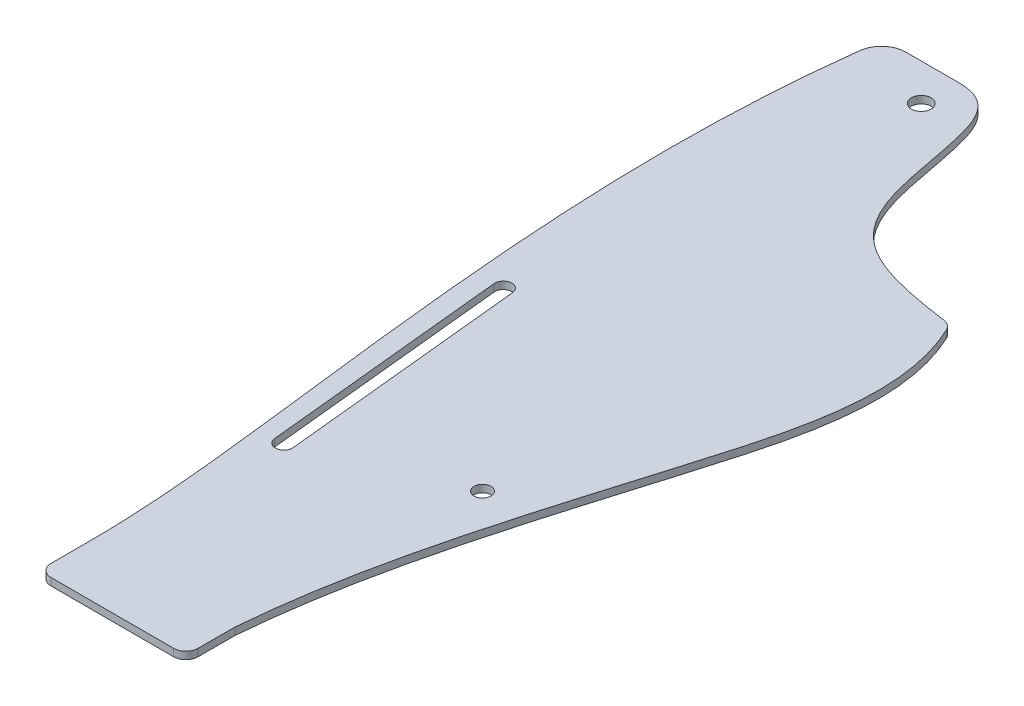
SolidWorks part; units mm, degrees
ref_plane "Front Plane" through (0, 0, 0) normal (0, 0, 1) x (1, 0, 0)
ref_plane "Top Plane" through (0, 0, 0) normal (0, 1, 0) x (1, 0, 0)
ref_plane "Right Plane" through (0, 0, 0) normal (1, 0, 0) x (0, 0, -1)
sketch "Sketch1" plane through (0, 0, 0) normal (0, 1, 0) x (1, 0, 0)
  line L0 (0, 0) -> (0, -325) construction
  line L1 (0, -325) -> (-15, -325) construction
  line L2 (0, -325) -> (45, -325) construction
  line L3 (0, 0) -> (83.906, 0) construction
  line L4 (83.906, 0) -> (83.906, -72.3342) construction
  line L5 (-15, -325) -> (-15, -345)
  line L6 (-15, -345) -> (45, -345)
  line L7 (45, -345) -> (45, -325)
  line L8 (-10, -250) -> (-20, -150.5013) construction
  line L9 (-13.4825, -250.35) -> (-23.4825, -150.8513)
  line L10 (-6.5175, -249.65) -> (-16.5175, -150.1513)
  line L11 (0, 15) -> (-30, 15)
  circle A0 centre (0, 0) radius 15
  circle A1 centre (0, 0) radius 4
  arc A2 (-13.4825, -250.35) -> (-6.5175, -249.65) centre (-10, -250) ccw
  arc A3 (-16.5175, -150.1513) -> (-23.4825, -150.8513) centre (-20, -150.5013) ccw
  circle A4 centre (47.5, -226.5) radius 3.45
  spline S0 degree 3 poles (-30, 15) (-42.0279, -69.7185) (-28.6476, -182.4063) (-15, -295.8488) (-15, -325) knots 0 0 0 0 0.742443 1 1 1 1
  spline S1 degree 3 poles (0, 15) (11.8595, 15) (19.028, 4.9911) (28.0688, -60.3575) (48.2185, -67.4795) (83.906, -72.3342) knots 0 0 0 0 0.292385 0.473699 1 1 1 1
  spline S2 degree 3 poles (83.906, -72.3342) (100.0677, -103.7836) (75.9963, -191.9592) (49.5675, -271.3641) (45, -325) knots 0 0 0 0 0.388668 1 1 1 1
  point P14 (-15, -200.2506)
  dimension "D1" = 30
  dimension "D2" = 8
  dimension "D12" = 3.5
  dimension "D14" = 6.9
  dimension "D3" = 325
  dimension "D4" = 15
  dimension "D5" = 45
  dimension "D8" = 20
  dimension "D9" = 10
  dimension "D10" = 20
  dimension "D11" = 100
  dimension "D13" = 75
  dimension "D15" = 47.5
  dimension "D16" = 226.5
  dimension "D17" = 30
  dimension "D18" = 92
  dimension "D19" = 81
  dimension "D20" = 54
extrude "Boss-Extrude1" add sketch "Sketch1" along normal blind 3
fillet "Fillet1" radius 5 3 edges at (83.906, 1.5, 72.3342) (45, 1.5, 345) (-15, 1.5, 345)
fillet "Fillet2" radius 10 1 edges at (-30, 1.5, -15)
